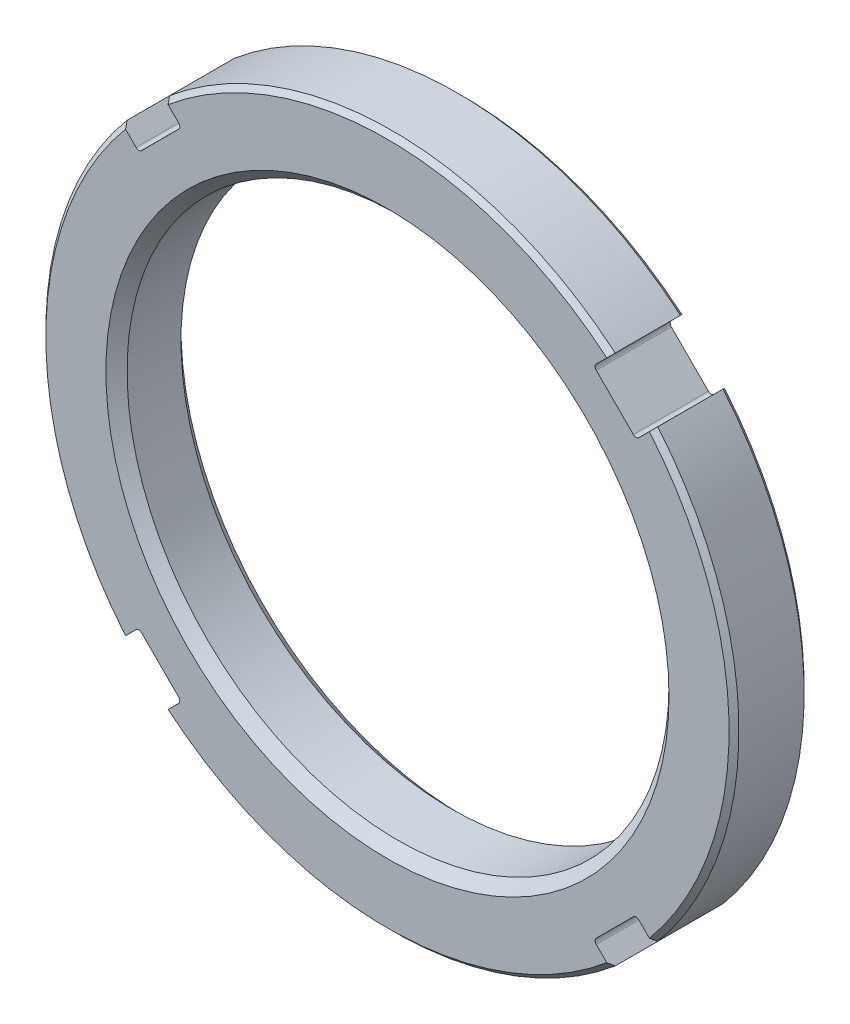
SolidWorks part; units mm, degrees
material "Alloy Steel"
ref_plane "Front Plane" through (0, 0, 0) normal (0, 0, 1) x (1, 0, 0)
ref_plane "Top Plane" through (0, 0, 0) normal (0, 1, 0) x (1, 0, 0)
ref_plane "Right Plane" through (0, 0, 0) normal (1, 0, 0) x (0, 0, -1)
sketch "Sketch1" plane through (0, 0, 0) normal (0, 0, 1) x (1, 0, 0)
  circle A0 centre (0, 0) radius 36.576
  circle A1 centre (0, 0) radius 28.6004
  dimension "D1" = 73.152
  dimension "D2" = 57.2008
extrude "Extrude1" add sketch "Sketch1" along normal blind 7.9248
chamfer "Chamfer1" distance 0.5192 angle 45 2 edges at (36.576, 0, 0) (36.576, 0, 7.9248)
chamfer "Chamfer2" distance 1.1176 angle 45 2 edges at (28.6004, 0, 0) (28.6004, 0, 7.9248)
sketch "Sketch2" plane through (0, 0, 7.9248) normal (0, 0, 1) x (1, 0, 0)
  line L0 (0, 0) -> (22.7176, 0) construction
  line L1 (0, 0) -> (15.6425, 15.6425) construction
  line L2 (23.5204, 28.0106) -> (21.7502, 26.2403)
  line L3 (21.7502, 26.2403) -> (26.2403, 21.7502)
  line L4 (28.0106, 23.5204) -> (26.2403, 21.7502)
  circle A0 centre (0, 0) radius 36.576 construction
  arc A1 (28.0106, 23.5204) -> (23.5204, 28.0106) centre (0, 0) ccw
  dimension "D3" = 2.6416
  dimension "D1" = 45
  dimension "D2" = 6.35
extrude "Cut-Extrude1" cut sketch "Sketch2" against normal through all
fillet "Fillet1" radius 0.4064 2 edges at (26.2403, 21.7502, 3.9624) (21.7502, 26.2403, 3.9624)
pattern_circular "CirPattern1" count 4 over 360 about axis through (0, 0, 0) along (0, 0, 1) of "Fillet1", "Cut-Extrude1"
